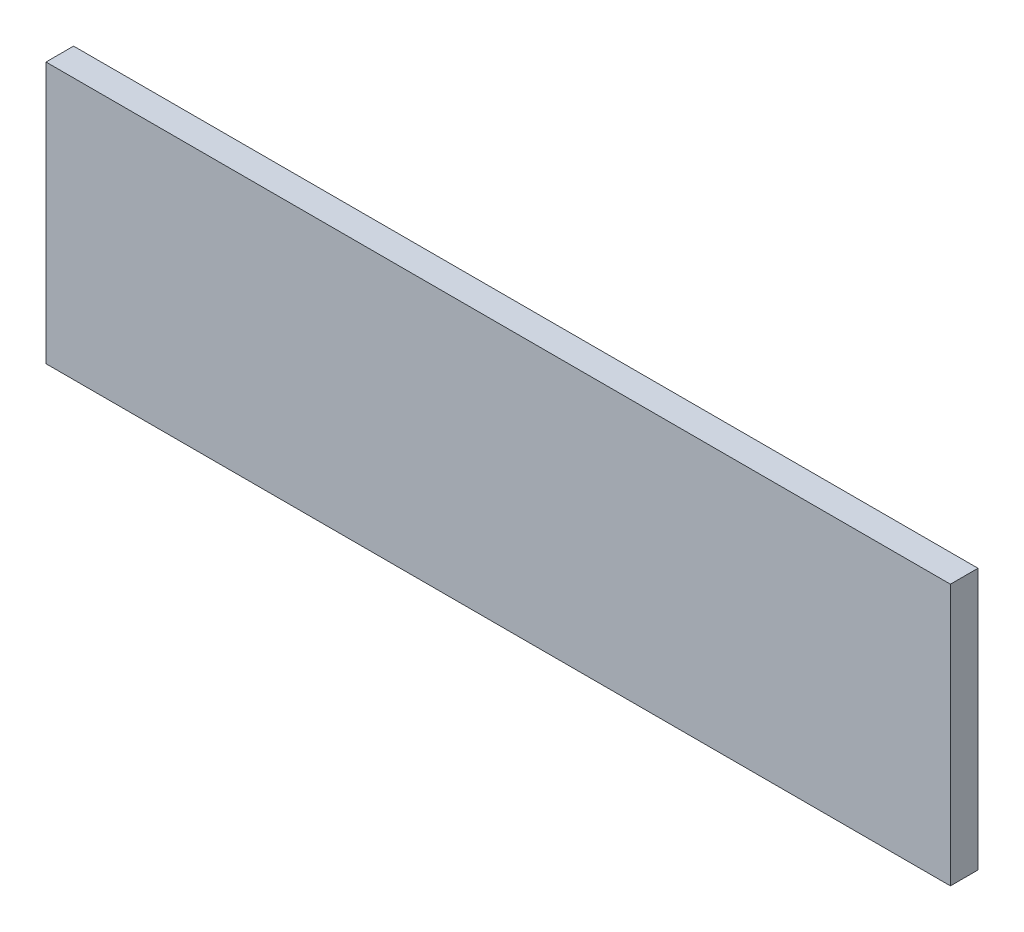
SolidWorks part; units mm, degrees
ref_plane "Ebene vorne" through (0, 0, 0) normal (0, 0, 1) x (1, 0, 0)
ref_plane "Ebene oben" through (0, 0, 0) normal (0, 1, 0) x (1, 0, 0)
ref_plane "Ebene rechts" through (0, 0, 0) normal (1, 0, 0) x (0, 0, -1)
sketch "Skizze1" plane through (0, 0, 0) normal (0, 0, 1) x (1, 0, 0)
  line L1 (311.5, -90) -> (-311.5, -90)
  line L2 (311.5, -90) -> (311.5, 90)
  line L3 (311.5, 90) -> (-311.5, 90)
  line L4 (-311.5, -90) -> (-311.5, 90)
  line L5 (311.5, -90) -> (-311.5, 90) construction
  line L6 (311.5, 90) -> (-311.5, -90) construction
  point P0 (0, 0)
  dimension "D1" = 623
  dimension "D2" = 180
extrude "Aufsatz-Linear austragen1" add sketch "Skizze1" along normal blind 19
